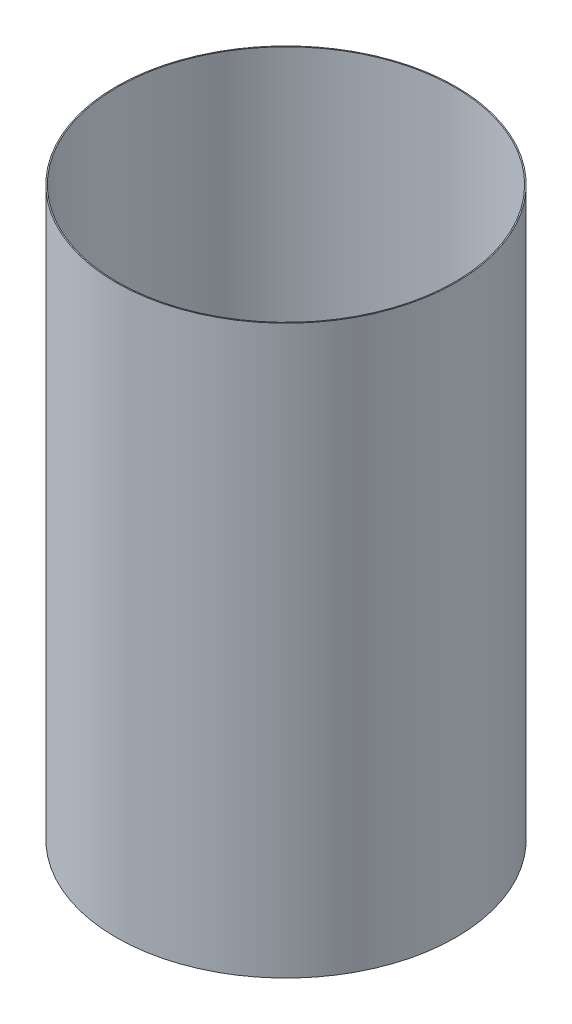
SolidWorks part; units mm, degrees
material "Thornel Mat VMA"
ref_plane "Front Plane" through (0, 0, 0) normal (0, 0, 1) x (1, 0, 0)
ref_plane "Top Plane" through (0, 0, 0) normal (0, 1, 0) x (1, 0, 0)
ref_plane "Right Plane" through (0, 0, 0) normal (1, 0, 0) x (0, 0, -1)
ref_axis "Axis1" through (0, 55, 0) along (0, -1, 0)
sketch "Sketch1" plane through (0, 0, 0) normal (0, 0, 1) x (1, 0, 0)
  line L0 (-39.6811, -69.0032) -> (-39.6811, -202.3532)
  line L2 (-38.1, -202.3532) -> (0, -202.3532) construction
  line L3 (-38.1, -69.0032) -> (0, -69.0032) construction
revolve "Revolve-Thin1" add sketch "Sketch1" angle 360 about axis through (0, 55, 0) along (0, -1, 0)
equation "\"D3@Revolve-Thin1\"=\"CF THICKNESS@Cryo Tank.Assembly\""
